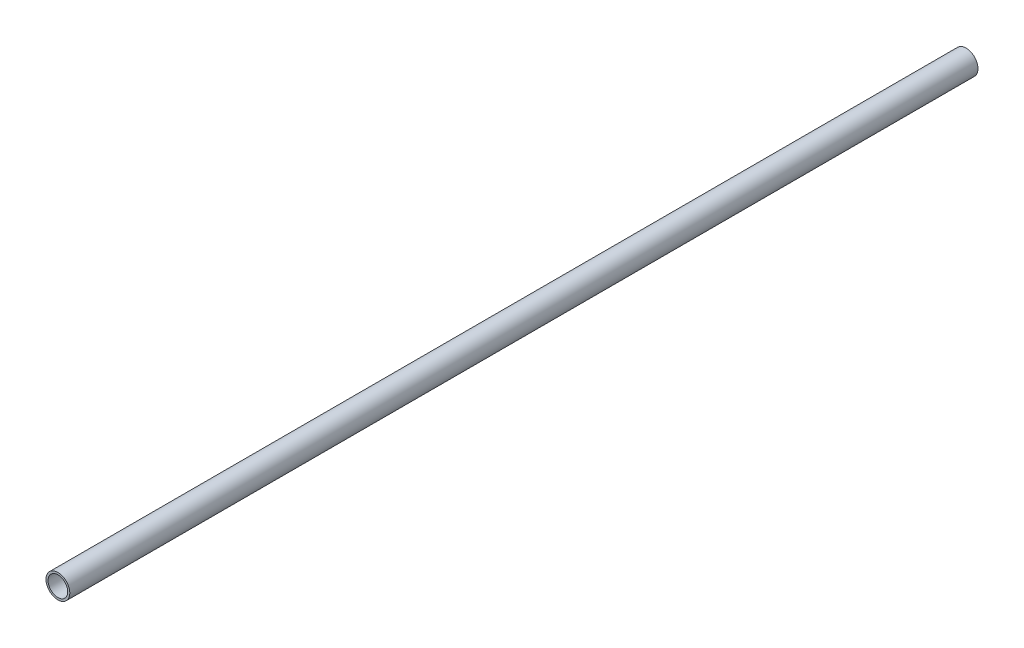
SolidWorks part; units mm, degrees
material "Hexcel AS4C (3000 Filaments)"
ref_plane "Front Plane" through (0, 0, 0) normal (0, 0, 1) x (1, 0, 0)
ref_plane "Top Plane" through (0, 0, 0) normal (0, 1, 0) x (1, 0, 0)
ref_plane "Right Plane" through (0, 0, 0) normal (1, 0, 0) x (0, 0, -1)
sketch "Sketch1" plane through (0, 0, 0) normal (0, 0, 1) x (1, 0, 0)
  circle A0 centre (0, 0) radius 5.9944
  circle A1 centre (0, 0) radius 4.953
  dimension "D1" = 11.9888
  dimension "D2" = 9.906
extrude "Boss-Extrude1" add sketch "Sketch1" along normal blind 457.2
sketch "Sketch8" plane through (0, 0, 0) normal (0, 0, -1) x (-1, 0, 0)
  circle A0 centre (0, 0) radius 5.1435
  dimension "D1" = 10.287
extrude "Cut-Extrude2" [suppressed] cut sketch "Sketch8" against normal blind 25.4
sketch "Sketch9" plane through (0, 0, 457.2) normal (0, 0, 1) x (1, 0, 0)
  circle A0 centre (0, 0) radius 5.1435
  dimension "D1" = 10.287
extrude "Cut-Extrude3" [suppressed] cut sketch "Sketch9" against normal blind 25.4
ref_plane "Plane1" [suppressed] through (-5.9944, 0, 0) normal (-1, 0, 0) x (0, 0, 1)
hole_wizard "1/8 (0.125) Diameter Hole1" [suppressed] positions "Sketch11" profile "Sketch12" hole size "1/8" standard "ANSI Inch"
sketch "Sketch11" [suppressed] plane through (-5.9944, 0, 0) normal (-1, 0, 0) x (0, 0, 1)
  line L0 (0, 0) -> (457.2, 0) construction
  line L2 (457.2, -5.9944) -> (457.2, 5.9944) construction
  point P0 (452.4375, 0)
  point P2 (4.7625, 0)
  dimension "D1" = 4.7625
  dimension "D2" = 4.7625
sketch "Sketch12" plane through (-5.9944, 0, 452.4375) normal (0, 1, 0) x (0, 0, 1)
  line L0 (0, 0) -> (0, 11.9888)
  line L1 (0, 11.9888) -> (1.5875, 11.9888)
  line L2 (1.5875, 11.9888) -> (1.5875, 0)
  line L5 (1.5875, 0) -> (0, 0)
  line L11 (0, -6.35) -> (0, 107.95) construction
  dimension "Thru Hole Dia." = 3.175
  dimension "Thru Hole Depth" = 11.9888
